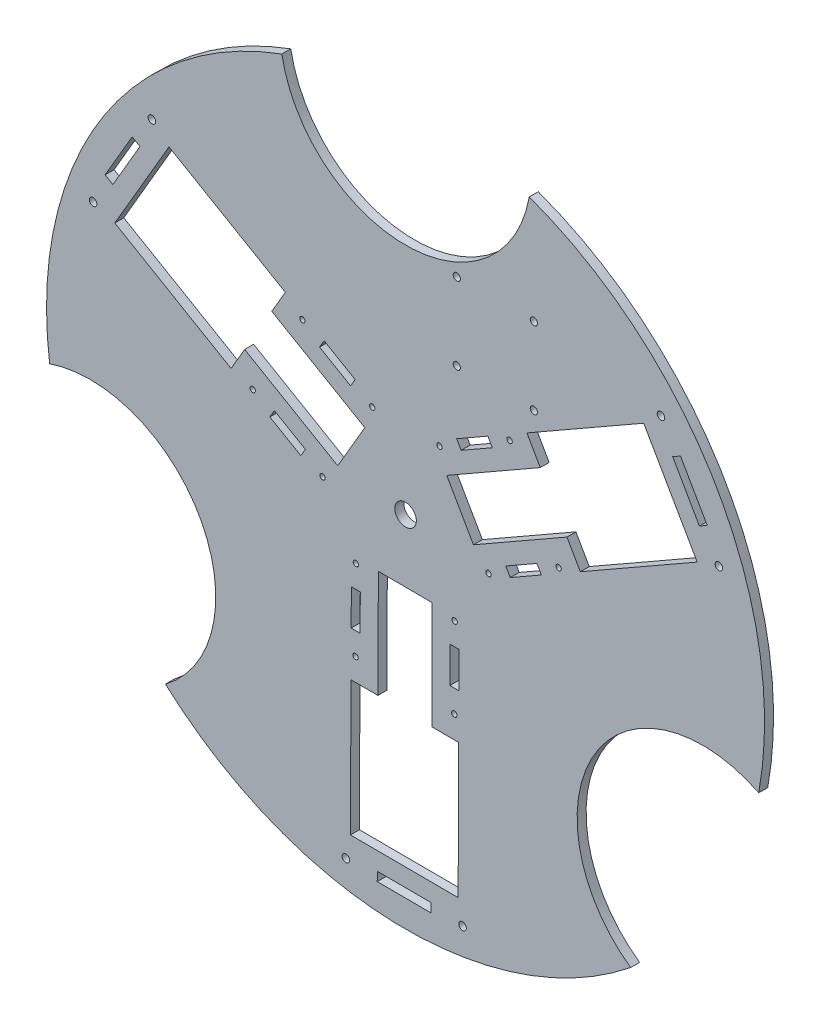
SolidWorks part; units mm, degrees
ref_plane "Front Plane" through (0, 0, 0) normal (0, 0, 1) x (1, 0, 0)
ref_plane "Top Plane" through (0, 0, 0) normal (0, 1, 0) x (1, 0, 0)
ref_plane "Right Plane" through (0, 0, 0) normal (1, 0, 0) x (0, 0, -1)
sketch "Sketch1" plane through (0, 0, 0) normal (0, 0, 1) x (1, 0, 0)
  arc A0 (-133.7687, -148.6806) -> (125.3956, -155.8074) centre (0, 0) ccw
  arc A1 (-68.9198, 187.75) -> (68.9198, 187.75) centre (0, 200) ccw
  arc A2 (196.7661, -35.8206) -> (125.3956, -155.8074) centre (165.5758, -98.4877) ccw
  arc A3 (-133.7687, -148.6806) -> (-198.2544, -26.3664) centre (-175.71, -92.6366) ccw
  arc A4 (-68.9198, 187.75) -> (-198.2544, -26.3664) centre (0, 0) ccw
  arc A5 (196.7661, -35.8206) -> (68.9198, 187.75) centre (0, 0) ccw
  point P11 (-3.3781, 2.9586)
  dimension "D1" = 400
  dimension "D2" = 140
extrude "Boss-Extrude1" add sketch "Sketch1" along normal blind 5
sketch "Sketch2" plane through (0, 0, 5) normal (0, 0, 1) x (1, 0, 0)
  circle A0 centre (0, 0) radius 6
  dimension "D1" = 12
extrude "Cut-Extrude1" cut sketch "Sketch2" against normal through all
sketch "Sketch3" plane through (0, 0, 5) normal (0, 0, 1) x (1, 0, 0)
  line L0 (173.618, 99.2814) -> (0, 0) construction
  line L1 (-0.8287, -199.9983) -> (0, 0) construction
  line L2 (-172.7892, 100.7168) -> (0, 0) construction
  line L3 (-131.7633, 111.5277) -> (-66.9674, 73.7589)
  line L4 (-161.9784, 59.6909) -> (-97.1824, 21.9221)
  line L5 (-131.7633, 111.5277) -> (-161.9784, 59.6909)
  line L6 (-66.9674, 73.7589) -> (-74.5211, 60.7997)
  line L7 (-74.5211, 60.7997) -> (-22.6844, 30.5846)
  line L8 (-97.1824, 21.9221) -> (-89.6286, 34.8813)
  line L9 (-89.6286, 34.8813) -> (-37.7919, 4.6663)
  line L10 (-22.6844, 30.5846) -> (-37.7919, 4.6663)
  line L11 (162.4675, 58.3465) -> (97.3607, 21.116)
  line L12 (132.683, 110.4319) -> (67.5763, 73.2014)
  line L13 (162.4675, 58.3465) -> (132.683, 110.4319)
  line L14 (97.3607, 21.116) -> (89.9146, 34.1373)
  line L15 (89.9146, 34.1373) -> (37.8293, 4.3529)
  line L16 (67.5763, 73.2014) -> (75.0224, 60.18)
  line L17 (75.0224, 60.18) -> (22.937, 30.3956)
  line L18 (37.8293, 4.3529) -> (22.937, 30.3956)
  line L19 (173.618, 99.2814) -> (0, 0) construction
  line L20 (-30.7042, -169.8742) -> (-30.3934, -94.8749)
  line L21 (29.2953, -170.1228) -> (29.6061, -95.1235)
  line L22 (-30.7042, -169.8742) -> (29.2953, -170.1228)
  line L23 (-30.3934, -94.8749) -> (-15.3935, -94.937)
  line L24 (-15.3935, -94.937) -> (-15.1449, -34.9375)
  line L25 (29.6061, -95.1235) -> (14.6062, -95.0613)
  line L26 (14.6062, -95.0613) -> (14.8548, -35.0619)
  line L27 (-15.1449, -34.9375) -> (14.8548, -35.0619)
  line L28 (-0.8287, -199.9983) -> (0, 0) construction
  arc A0 (196.7661, -35.8206) -> (68.9198, 187.75) centre (0, 0) ccw construction
  point P10 (0, 0)
  point P22 (0, 0)
  point P32 (0, 0)
  point P39 (0, 0)
  dimension "D2" = 75
  dimension "D3" = 30
  dimension "D4" = 30
  dimension "D5" = 60
  dimension "D6" = 15
  dimension "D1" = 3
extrude "Cut-Extrude3" cut sketch "Sketch3" against normal through all
sketch "Sketch4" plane through (0, 0, 5) normal (0, 0, 1) x (1, 0, 0)
  line L0 (-75.5838, 9.3325) -> (-73.0658, 13.6522)
  line L1 (-73.0658, 13.6522) -> (-55.7869, 3.5806)
  line L2 (-55.7869, 3.5806) -> (-58.3048, -0.7392)
  line L3 (-58.3048, -0.7392) -> (-75.5838, 9.3325)
  line L4 (-47.8866, 56.8495) -> (-45.3687, 61.1693)
  line L5 (-45.3687, 61.1693) -> (-28.0898, 51.0976)
  line L6 (-28.0898, 51.0976) -> (-30.6077, 46.7779)
  line L7 (-30.6077, 46.7779) -> (-47.8866, 56.8495)
  line L8 (45.8741, 60.7912) -> (48.3561, 56.4508)
  line L9 (48.3561, 56.4508) -> (30.9943, 46.5226)
  line L10 (30.9943, 46.5226) -> (28.5123, 50.8631)
  line L11 (28.5123, 50.8631) -> (45.8741, 60.7912)
  line L12 (73.1765, 13.0463) -> (75.6585, 8.7058)
  line L13 (75.6585, 8.7058) -> (58.2967, -1.2223)
  line L14 (58.2967, -1.2223) -> (55.8147, 3.1181)
  line L15 (55.8147, 3.1181) -> (73.1765, 13.0463)
  line L16 (29.7097, -70.1237) -> (24.7097, -70.103)
  line L17 (24.7097, -70.103) -> (24.7926, -50.1032)
  line L18 (24.7926, -50.1032) -> (29.7926, -50.1239)
  line L19 (29.7926, -50.1239) -> (29.7097, -70.1237)
  line L20 (-25.2898, -69.8958) -> (-30.2898, -69.8751)
  line L21 (-30.2898, -69.8751) -> (-30.2069, -49.8753)
  line L22 (-30.2069, -49.8753) -> (-25.207, -49.896)
  line L23 (-25.207, -49.896) -> (-25.2898, -69.8958)
  circle A0 centre (-57.427, 65.3042) radius 1.5
  circle A1 centre (-18.5494, 42.6429) radius 1.5
  circle A2 centre (-46.2465, -4.8741) radius 1.5
  circle A3 centre (-85.1241, 17.7872) radius 1.5
  circle A4 centre (85.2686, 17.0811) radius 1.5
  circle A5 centre (46.2046, -5.2572) radius 1.5
  circle A6 centre (18.9022, 42.4877) radius 1.5
  circle A7 centre (57.9662, 64.8261) radius 1.5
  circle A8 centre (-27.8416, -82.3853) radius 1.5
  circle A9 centre (-27.6551, -37.3857) radius 1.5
  circle A10 centre (27.3444, -37.6136) radius 1.5
  circle A11 centre (27.1579, -82.6132) radius 1.5
  point P62 (0, 0)
extrude "Cut-Extrude4" cut sketch "Sketch4" against normal through all
sketch "Sketch5" plane through (0, 0, 5) normal (0, 0, 1) x (1, 0, 0)
  line L0 (0, 130) -> (0, 107.5) construction
  line L1 (50, 107.5) -> (0, 107.5) construction
  line L3 (25, 132.5) -> (75, 132.5) construction
  line L4 (25, 132.5) -> (25, 82.5) construction
  line L5 (25, 82.5) -> (75, 82.5) construction
  line L6 (75, 132.5) -> (75, 82.5) construction
  line L7 (25, 132.5) -> (75, 82.5) construction
  line L8 (25, 82.5) -> (75, 132.5) construction
  arc A0 (-68.9198, 187.75) -> (68.9198, 187.75) centre (0, 200) ccw construction
  circle A1 centre (71.4645, 128.9645) radius 2
  circle A2 centre (71.4645, 86.0355) radius 2
  circle A3 centre (28.5355, 86.0355) radius 2
  circle A4 centre (28.5355, 128.9645) radius 2
  point P23 (50, 107.5)
  dimension "D4" = 4
  dimension "D1" = 22.5
  dimension "D2" = 50
  dimension "D3" = 50
  dimension "D5" = 5
extrude "Cut-Extrude5" cut sketch "Sketch5" against normal through all
sketch "Sketch6" plane through (0, 0, 0) normal (0, 0, -1) x (-1, 0, 0)
  line L0 (140.2462, 121.7966) -> (142.3612, 118.1681) construction
  line L1 (142.406, 123.0556) -> (138.0863, 120.5377) construction
  line L2 (144.5211, 119.427) -> (140.2014, 116.9091) construction
  line L3 (175.0942, 62.0116) -> (172.9791, 65.6401) construction
  line L4 (177.2541, 63.2705) -> (172.9343, 60.7526) construction
  line L5 (175.139, 66.8991) -> (170.8193, 64.3812) construction
  line L6 (35.3559, -182.3551) -> (31.1559, -182.3725) construction
  line L7 (-33.8435, -182.6418) -> (-29.6435, -182.6244) construction
  line L8 (-175.6021, 60.5584) -> (-173.5172, 64.2044) construction
  line L9 (-141.2507, 120.6302) -> (-143.3356, 116.9843) construction
  line L10 (-148.81, 102.3747) -> (-153.1505, 104.8567)
  line L11 (-153.1505, 104.8567) -> (-168.0427, 78.814)
  line L12 (-168.0427, 78.814) -> (-163.7023, 76.332)
  line L13 (-163.7023, 76.332) -> (-148.81, 102.3747)
  line L14 (163.0641, 77.686) -> (167.3838, 80.2039)
  line L15 (167.3838, 80.2039) -> (152.2763, 106.1223)
  line L16 (152.2763, 106.1223) -> (147.9565, 103.6043)
  line L17 (147.9565, 103.6043) -> (163.0641, 77.686)
  line L18 (-14.254, -180.0606) -> (-14.2333, -185.0606)
  line L19 (-14.2333, -185.0606) -> (15.7664, -184.9363)
  line L20 (15.7664, -184.9363) -> (15.7457, -179.9363)
  line L21 (15.7457, -179.9363) -> (-14.254, -180.0606)
  circle A0 centre (141.3037, 119.9824) radius 2.1
  circle A1 centre (174.0367, 63.8259) radius 2.1
  circle A2 centre (33.2559, -182.3638) radius 2.1
  circle A3 centre (-31.7435, -182.6331) radius 2.1
  circle A4 centre (-174.5596, 62.3814) radius 2.1
  circle A5 centre (-142.2931, 118.8072) radius 2.1
  point P35 (0, 0)
  point P52 (0, 0)
extrude "Cut-Extrude6" cut sketch "Sketch6" against normal through all
